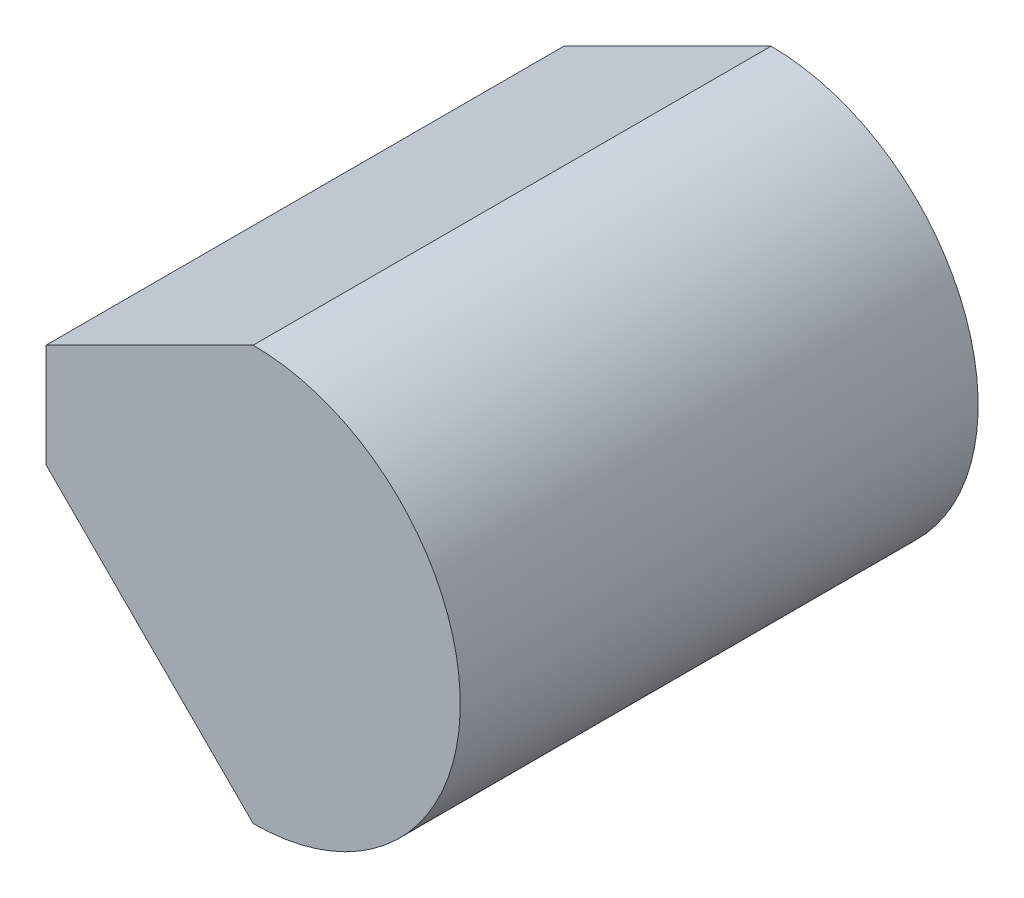
SolidWorks part; units mm, degrees
ref_plane "Front Plane" through (0, 0, 0) normal (0, 0, 1) x (1, 0, 0)
ref_plane "Top Plane" through (0, 0, 0) normal (0, 1, 0) x (1, 0, 0)
ref_plane "Right Plane" through (0, 0, 0) normal (1, 0, 0) x (0, 0, -1)
sketch "Sketch1" plane through (0, 0, 0) normal (0, 0, 1) x (1, 0, 0)
  line L0 (-10, 10) -> (-10, 15)
  line L1 (-10, 15) -> (0, 20)
  line L2 (-10, 10) -> (0, 0)
  arc A0 (0, 0) -> (0, 20) centre (0, 10) ccw
  dimension "D6" = 10
  dimension "D1" = 5
  dimension "D2" = 10
  dimension "D3" = 5
  dimension "D4" = 10
  dimension "D5" = 10
extrude "Boss-Extrude1" add sketch "Sketch1" along normal blind 25
